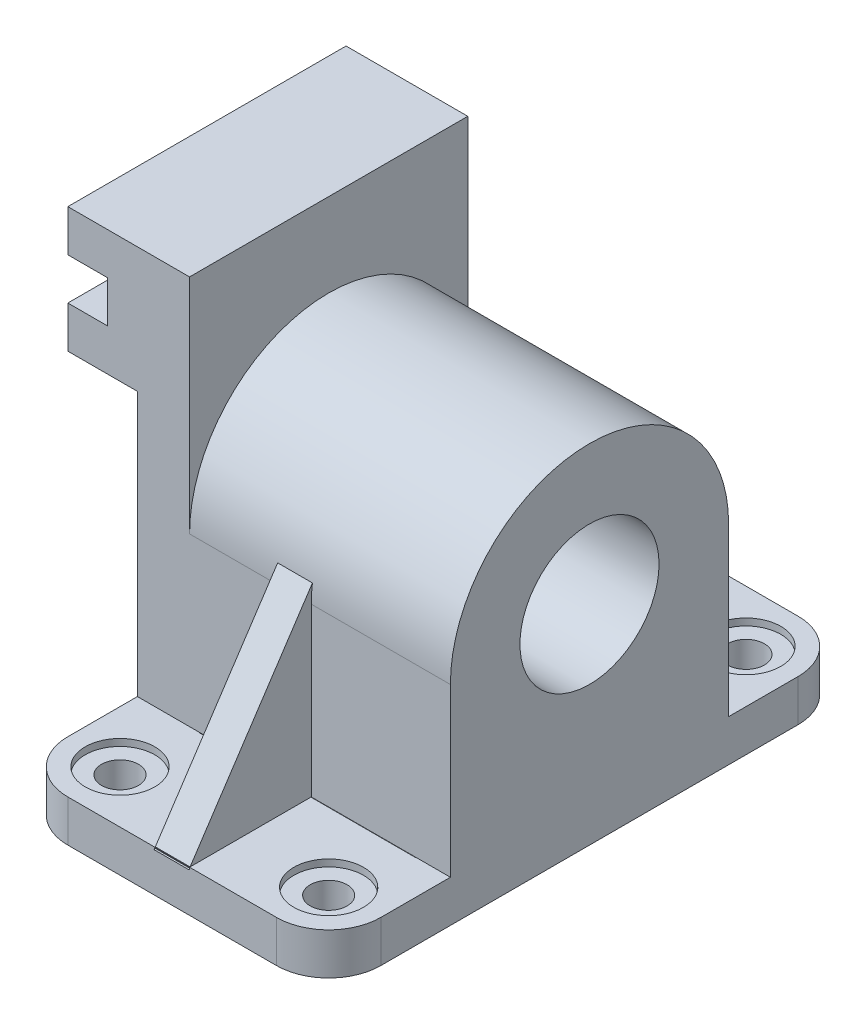
SolidWorks part; units mm, degrees
ref_plane "Alzado" through (0, 0, 0) normal (0, 0, 1) x (1, 0, 0)
ref_plane "Planta" through (0, 0, 0) normal (0, 1, 0) x (1, 0, 0)
ref_plane "Vista lateral" through (0, 0, 0) normal (1, 0, 0) x (0, 0, -1)
sketch "Croquis1" plane through (0, 0, 0) normal (1, 0, 0) x (0, 0, -1)
  line L0 (0, 0) -> (0, -57.4714) construction
  line L2 (-20, -24) -> (20, -24)
  line L3 (20, -24) -> (20, 0)
  line L5 (-20, 0) -> (-20, -24)
  circle A0 centre (0, 0) radius 10
  arc A1 (20, 0) -> (-20, 0) centre (0, 0) ccw
  point P16 (0, -30)
  dimension "D1" = 40
  dimension "D2" = 20
  dimension "D3" = 40
extrude "Saliente-Extruir1" add sketch "Croquis1" along normal mid plane 45
ref_plane "Plano1" through (0, -24, 0) normal (0, -1, 0) x (-1, 0, 0)
sketch "Croquis3" plane through (0, -24, 0) normal (0, -1, 0) x (-1, 0, 0)
  line L0 (22.5, 30) -> (22.5, 18.7498)
  line L1 (15, 37.5) -> (-15, 37.5)
  line L2 (22.5, -20) -> (22.5, 20) construction
  line L3 (-22.5, 20) -> (22.5, 20) construction
  line L4 (22.5, 18.7498) -> (22.5, -30)
  line L5 (15, -37.5) -> (-15, -37.5)
  line L6 (-22.5, 30) -> (-22.5, -30)
  arc A0 (22.5, 30) -> (15, 37.5) centre (15, 30) ccw
  arc A1 (-15, 37.5) -> (-22.5, 30) centre (-15, 30) ccw
  circle A2 centre (15, 30) radius 2.65
  circle A4 centre (-15, 30) radius 2.65
  arc A6 (22.5, -30) -> (15, -37.5) centre (15, -30) cw
  arc A7 (-15, -37.5) -> (-22.5, -30) centre (-15, -30) cw
  circle A8 centre (15, -30) radius 2.65
  circle A9 centre (-15, -30) radius 2.65
  dimension "D1" = 7.5
  dimension "D2" = 7.5
  dimension "D4" = 7.5
  dimension "D5" = 5.3
  dimension "D6" = 7.5
  dimension "D8" = 5.3
  dimension "D9" = 5.3
  dimension "D3" = 17.5
extrude "Saliente-Extruir2" add sketch "Croquis3" along normal blind 6
sketch "Croquis5" plane through (0, -24, 0) normal (0, -1, 0) x (-1, 0, 0)
  circle A0 centre (15, 30) radius 5
  circle A1 centre (-15, 30) radius 5
  circle A2 centre (15, -30) radius 5
  circle A3 centre (-15, -30) radius 5
  dimension "D1" = 10
extrude "Cortar-Extruir1" cut sketch "Croquis5" along normal blind 1
sketch "Croquis6" plane through (0, 0, 0) normal (0, 0, 1) x (1, 0, 0)
  line L0 (-15, -25) -> (-15, 21.3635) construction
  line L1 (-12.35, -25) -> (-17.65, -25) construction
  line L2 (-15, 20.0679) -> (-15, 32)
  line L3 (-15, 32) -> (-32.5, 32)
  line L4 (-32.5, 32) -> (-32.5, 26)
  line L5 (-32.5, 26) -> (-26.7873, 26)
  line L6 (-26.7873, 26) -> (-26.7873, 20)
  line L7 (-26.7873, 20) -> (-32.5, 20)
  line L8 (-32.5, 20) -> (-32.5, 14)
  line L9 (-32.5, 14) -> (-22.5, 14)
  line L10 (-22.5, 20) -> (-22.5, 0) construction
  line L11 (-22.5, 14) -> (-22.5, 0)
  line L12 (-22.5, 0) -> (-15, 0)
  line L13 (22.5, 0) -> (-22.5, 0) construction
  line L14 (-15, 0) -> (-15, 20.0679)
  dimension "D1" = 17.5
  dimension "D2" = 6
  dimension "D3" = 6
  dimension "D4" = 32
  dimension "D5" = 6
extrude "Saliente-Extruir3" add sketch "Croquis6" along normal mid plane 40
sketch "Croquis8" plane through (-22.5, 0, 0) normal (-1, 0, 0) x (0, 0, 1)
  line L0 (10, 0) -> (-10, 0) construction
  circle A0 centre (0, 0) radius 10
  dimension "D1" = 20
extrude "Cortar-Extruir2" cut sketch "Croquis8" against normal blind 45
sketch "Croquis10" plane through (0, 0, 0) normal (1, 0, 0) x (0, 0, -1)
  line L0 (-18.1388, 5.125) -> (-37.5985, -24.2653)
  line L1 (-37.5985, -24.2653) -> (-18.1388, -24.2653)
  line L2 (-18.1388, -24.2653) -> (-18.1388, 5.125)
  line L3 (37.0259, -24.2653) -> (19.9484, -24.2653)
  line L4 (19.9484, -24.2653) -> (19.9484, 5.125)
  line L5 (19.9484, 5.125) -> (37.0259, -24.2653)
extrude "Saliente-Extruir4" add sketch "Croquis10" along normal mid plane 5
sketch "Croquis15" plane through (0, -30, 0) normal (0, -1, 0) x (1, 0, 0)
  line L0 (-13.6329, 20.0518) -> (-13.6329, -19.8089)
  line L4 (-13.6329, 20.0518) -> (17.5, 20.0518)
  line L5 (17.5, 20.0518) -> (17.5, -19.8089)
  line L6 (17.5, -19.8089) -> (-13.6329, -19.8089)
  line L7 (22.5, -30) -> (22.5, 30) construction
  dimension "D1" = 5
extrude "Cortar-Extruir3" cut sketch "Croquis15" against normal blind 6
sketch "Croquis16" plane through (22.5, 0, 0) normal (1, 0, 0) x (0, 0, -1)
  line L0 (-20, -20) -> (-7.3139, -20)
  line L1 (-20, 0) -> (-20, -24) construction
  line L4 (-20, -24) -> (-20, 0) construction
  line L5 (-20, -6.8196) -> (-20, -20)
  line L6 (30, -30) -> (-30, -30) construction
  line L7 (-7.3139, -20) -> (-7.3139, -6.8196)
  line L8 (-20, -6.8196) -> (-7.3139, -6.8196)
  circle A1 centre (0, 0) radius 10 construction
  dimension "D1" = 10
